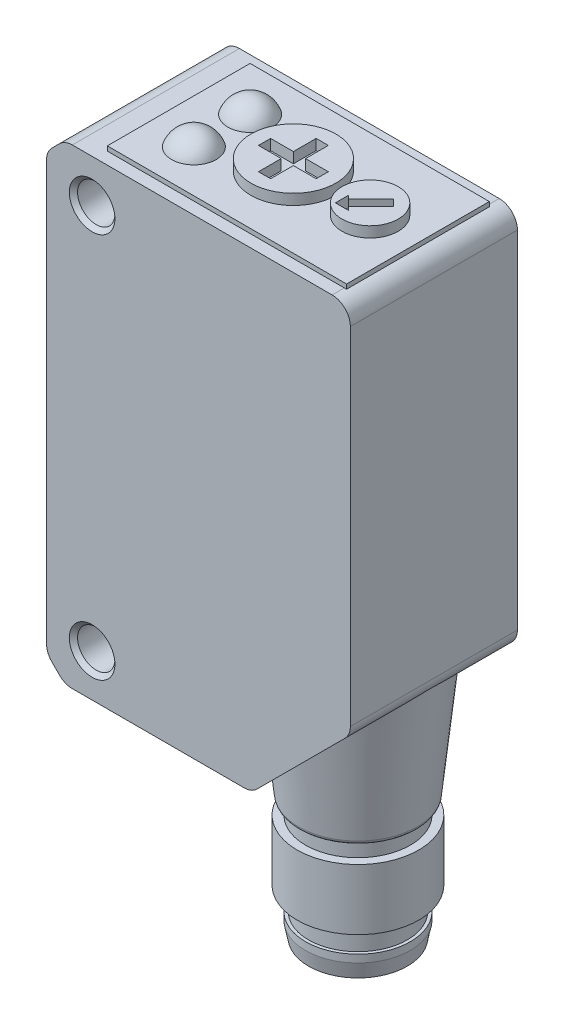
SolidWorks part; units mm, degrees
ref_plane "Front Plane" through (0, 0, 0) normal (0, 0, 1) x (1, 0, 0)
ref_plane "Top Plane" through (0, 0, 0) normal (0, 1, 0) x (1, 0, 0)
ref_plane "Right Plane" through (0, 0, 0) normal (1, 0, 0) x (0, 0, -1)
ref_plane "Plane1" through (0, 0, 0) normal (0, 0, 1) x (1, 0, 0)
sketch "Sketch1" plane through (0, 0, 0) normal (0, 0, 1) x (1, 0, 0)
  line L0 (-3, 26.5029) -> (-3, -1.1029)
  line L1 (-2.6485, -1.9515) -> (-2.1515, -2.4485)
  line L2 (-1.3029, -2.8) -> (10.0029, -2.8)
  line L3 (10.8515, -2.4485) -> (16.6485, 3.3485)
  line L4 (17, 4.1971) -> (17, 27)
  line L5 (15.8, 28.2) -> (-1.3029, 28.2)
  line L6 (-2.1515, 27.8485) -> (-2.6485, 27.3515)
  arc A0 (-3, -1.1029) -> (-2.6485, -1.9515) centre (-1.8, -1.1029) ccw
  arc A1 (-2.1515, -2.4485) -> (-1.3029, -2.8) centre (-1.3029, -1.6) ccw
  arc A2 (10.0029, -2.8) -> (10.8515, -2.4485) centre (10.0029, -1.6) ccw
  arc A3 (16.6485, 3.3485) -> (17, 4.1971) centre (15.8, 4.1971) ccw
  arc A4 (17, 27) -> (15.8, 28.2) centre (15.8, 27) ccw
  arc A5 (-1.3029, 28.2) -> (-2.1515, 27.8485) centre (-1.3029, 27) ccw
  arc A6 (-2.6485, 27.3515) -> (-3, 26.5029) centre (-1.8, 26.5029) ccw
extrude "Boss-Extrude1" add sketch "Sketch1" against normal blind 11
ref_plane "Plane2" through (0, 0, -5.5) normal (0, 0, 1) x (1, 0, 0)
sketch "Sketch2" plane through (0, 0, -5.5) normal (0, 0, 1) x (1, 0, 0)
  line L0 (12, 4.7) -> (16.8991, 4.7)
  line L1 (16.8991, 4.7) -> (15.8973, -4.8314)
  line L2 (15.599, -5.1) -> (15.45, -5.1)
  line L3 (15.45, -5.1) -> (15.45, -6.1)
  line L4 (15.45, -6.1) -> (16, -6.1)
  line L5 (16, -6.1) -> (16, -10.1)
  line L6 (16, -10.1) -> (15.25, -10.1)
  line L7 (15.25, -10.1) -> (15.25, -11.6)
  line L8 (15.25, -11.6) -> (15.45, -11.6)
  line L9 (15.45, -11.6) -> (15.45, -12.1)
  line L10 (15.45, -12.1) -> (15.25, -13.1)
  line L11 (15.25, -13.1) -> (12, -13.1)
  line L12 (12, -13.1) -> (12, 4.7)
  line L13 (12, -13.1) -> (12, 4.7) construction
  arc A0 (15.8973, -4.8314) -> (15.599, -5.1) centre (15.599, -4.8) cw
revolve "Revolve1" add sketch "Sketch2" angle 360 about L13
cosmetic thread "Cosmetic Thread1" parameters "D1"=4, "D2"=6.466
ref_plane "Plane3" through (0, -9.3, 0) normal (0, 1, 0) x (1, 0, 0)
sketch "Sketch3" plane through (0, -9.3, 0) normal (0, 1, 0) x (1, 0, 0)
  circle A0 centre (12, 5.5) radius 2.9
  circle A1 centre (13.4158, 4.4714) radius 0.5
  circle A2 centre (13.4158, 6.5286) radius 0.5
  circle A3 centre (11.4592, 3.8357) radius 0.5
  circle A4 centre (11.4592, 7.1643) radius 0.5
extrude "Cut-Extrude1" cut sketch "Sketch3" against normal blind 4
ref_plane "Plane4" through (0, 28.2, 0) normal (0, 1, 0) x (1, 0, 0)
sketch "Sketch4" plane through (0, 28.2, 0) normal (0, 1, 0) x (1, 0, 0)
  line L0 (0.2, 10.2) -> (0.2, 0.8)
  line L1 (0.2, 0.8) -> (15.95, 0.8)
  line L2 (15.95, 0.8) -> (15.95, 10.2)
  line L3 (15.95, 10.2) -> (0.2, 10.2)
  line L4 (11.6565, 4.3565) -> (12.5293, 4.3565)
  line L5 (12.5293, 4.3565) -> (12.305, 4.5808)
  line L6 (12.305, 4.5808) -> (13.7899, 6.0657)
  line L7 (13.7899, 6.0657) -> (13.3657, 6.4899)
  line L8 (13.3657, 6.4899) -> (11.8808, 5.005)
  line L9 (11.8808, 5.005) -> (11.6565, 5.2293)
  line L10 (11.6565, 5.2293) -> (11.6565, 4.3565)
  line L11 (5.85, 5.9) -> (5.85, 5.1)
  line L12 (5.85, 5.1) -> (7.35, 5.1)
  line L13 (7.35, 5.1) -> (7.35, 3.6)
  line L14 (7.35, 3.6) -> (8.15, 3.6)
  line L15 (8.15, 3.6) -> (8.15, 5.1)
  line L16 (8.15, 5.1) -> (9.65, 5.1)
  line L17 (9.65, 5.1) -> (9.65, 5.9)
  line L18 (9.65, 5.9) -> (8.15, 5.9)
  line L19 (8.15, 5.9) -> (8.15, 7.4)
  line L20 (8.15, 7.4) -> (7.35, 7.4)
  line L21 (7.35, 7.4) -> (7.35, 5.9)
  line L22 (7.35, 5.9) -> (5.85, 5.9)
extrude "Boss-Extrude2" add sketch "Sketch4" along normal blind 1
ref_plane "Plane5" through (0, 28.2, 0) normal (0, 1, 0) x (1, 0, 0)
sketch "Sketch5" plane through (0, 28.2, 0) normal (0, 1, 0) x (1, 0, 0)
  line L0 (0.2, 10.2) -> (0.2, 0.8)
  line L1 (0.2, 0.8) -> (15.95, 0.8)
  line L2 (15.95, 0.8) -> (15.95, 10.2)
  line L3 (15.95, 10.2) -> (0.2, 10.2)
  circle A0 centre (12.8, 5.5) radius 1.85
  circle A1 centre (7.75, 5.5) radius 2.8
extrude "Cut-Extrude2" cut sketch "Sketch5" along normal blind 1
ref_plane "Plane6" through (0, 28.2, 0) normal (0, 1, 0) x (1, 0, 0)
sketch "Sketch6" plane through (0, 28.2, 0) normal (0, 1, 0) x (1, 0, 0)
  line L0 (0.2, 10.2) -> (0.2, 0.8)
  line L1 (0.2, 0.8) -> (15.95, 0.8)
  line L2 (15.95, 0.8) -> (15.95, 10.2)
  line L3 (15.95, 10.2) -> (0.2, 10.2)
extrude "Boss-Extrude3" add sketch "Sketch6" along normal blind 0.3
ref_plane "Plane7" through (3.1, 0, 0) normal (1, 0, 0) x (0, 0, -1)
sketch "Sketch7" plane through (3.1, 0, 0) normal (1, 0, 0) x (0, 0, -1)
  line L0 (8.85, 28) -> (5.75, 28)
  line L1 (8.85, 28) -> (5.75, 28) construction
  arc A0 (5.75, 28) -> (8.85, 28) centre (7.3, 28) cw
revolve "Revolve2" add sketch "Sketch7" angle 360 about L1
ref_plane "Plane8" through (-2.8, 0, 0) normal (1, 0, 0) x (0, 0, -1)
sketch "Sketch8" plane through (-2.8, 0, 0) normal (1, 0, 0) x (0, 0, -1)
  line L0 (1.425, 19.925) -> (1.425, 2.675)
  line L1 (2.225, 1.875) -> (8.775, 1.875)
  line L2 (9.575, 2.675) -> (9.575, 19.925)
  line L3 (8.775, 20.725) -> (2.225, 20.725)
  arc A0 (1.425, 2.675) -> (2.225, 1.875) centre (2.225, 2.675) ccw
  arc A1 (8.775, 1.875) -> (9.575, 2.675) centre (8.775, 2.675) ccw
  arc A2 (9.575, 19.925) -> (8.775, 20.725) centre (8.775, 19.925) ccw
  arc A3 (2.225, 20.725) -> (1.425, 19.925) centre (2.225, 19.925) ccw
extrude "Cut-Extrude3" cut sketch "Sketch8" against normal blind 0.2
ref_plane "Plane9" through (0, 0, -11) normal (0, 0, 1) x (1, 0, 0)
sketch "Sketch9" plane through (0, 0, -11) normal (0, 0, 1) x (1, 0, 0)
  line L0 (4.4, 0.2) -> (9.0917, 0.2)
  line L1 (9.3745, 0.3172) -> (13.8828, 4.8255)
  line L2 (14, 5.1083) -> (14, 24.8)
  line L3 (13.6, 25.2) -> (4.4, 25.2)
  line L4 (4, 24.8) -> (4, 0.6)
  arc A0 (4, 0.6) -> (4.4, 0.2) centre (4.4, 0.6) ccw
  arc A1 (9.0917, 0.2) -> (9.3745, 0.3172) centre (9.0917, 0.6) ccw
  arc A2 (13.8828, 4.8255) -> (14, 5.1083) centre (13.6, 5.1083) ccw
  arc A3 (14, 24.8) -> (13.6, 25.2) centre (13.6, 24.8) ccw
  arc A4 (4.4, 25.2) -> (4, 24.8) centre (4.4, 24.8) ccw
extrude "Cut-Extrude4" cut sketch "Sketch9" along normal blind 0.1
ref_plane "Plane10" through (0, 0, 0) normal (1, 0, 0) x (0, 0, -1)
sketch "Sketch10" plane through (0, 0, 0) normal (1, 0, 0) x (0, 0, -1)
  line L0 (0, 0) -> (0, 1.5)
  line L1 (0, 1.5) -> (0.2705, 1.2295)
  line L2 (0.2705, 1.2295) -> (10.7295, 1.2295)
  line L3 (10.7295, 1.2295) -> (11, 1.5)
  line L4 (11, 1.5) -> (11, 0)
  line L5 (11, 0) -> (0, 0)
  line L6 (11, 0) -> (0, 0) construction
revolve "Cut-Revolve1" cut sketch "Sketch10" angle 360 about L6
cosmetic thread "Cosmetic Thread2" parameters "D1"=11, "D2"=3
ref_plane "Plane11" through (0, 0, 0) normal (1, 0, 0) x (0, 0, -1)
sketch "Sketch11" plane through (0, 0, 0) normal (1, 0, 0) x (0, 0, -1)
  line L0 (0, 25.4) -> (0, 26.9)
  line L1 (0, 26.9) -> (0.2705, 26.6295)
  line L2 (0.2705, 26.6295) -> (10.7295, 26.6295)
  line L3 (10.7295, 26.6295) -> (11, 26.9)
  line L4 (11, 26.9) -> (11, 25.4)
  line L5 (11, 25.4) -> (0, 25.4)
  line L6 (11, 25.4) -> (0, 25.4) construction
revolve "Cut-Revolve2" cut sketch "Sketch11" angle 360 about L6
cosmetic thread "Cosmetic Thread3" parameters "D1"=11, "D2"=3
ref_plane "Plane12" through (3.1, 0, 0) normal (1, 0, 0) x (0, 0, -1)
sketch "Sketch12" plane through (3.1, 0, 0) normal (1, 0, 0) x (0, 0, -1)
  line L0 (5.15, 28) -> (2.05, 28)
  line L1 (5.15, 28) -> (2.05, 28) construction
  arc A0 (2.05, 28) -> (5.15, 28) centre (3.6, 28) cw
revolve "Revolve3" add sketch "Sketch12" angle 360 about L1
ref_plane "Plane13" through (0.2, 28.5, -0.8) normal (1, 0, 0) x (0, 0, -1)
